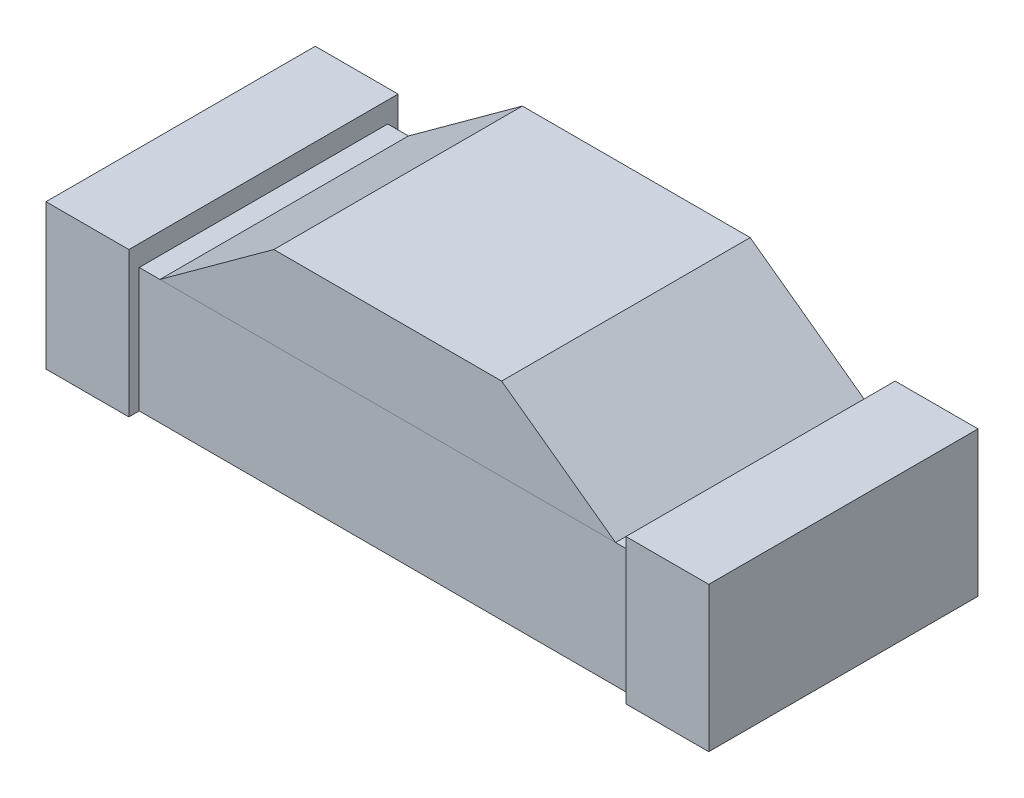
SolidWorks part; units mm, degrees
material "E-Glass Fiber"
ref_plane "Front Plane" through (0, 0, 0) normal (0, 0, 1) x (1, 0, 0)
ref_plane "Top Plane" through (0, 0, 0) normal (0, 1, 0) x (1, 0, 0)
ref_plane "Right Plane" through (0, 0, 0) normal (1, 0, 0) x (0, 0, -1)
sketch "Sketch1" plane through (0, 0, 0) normal (0, 1, 0) x (1, 0, 0)
  line L0 (-55, 0) -> (55, 0) construction
  line L1 (-0.75, 0.3) -> (0.75, 0.3)
  line L2 (-0.75, 0.3) -> (-0.75, 0.125)
  line L3 (-0.75, -0.3) -> (0.75, -0.3)
  line L4 (0.75, 0.3) -> (0.75, 0.125)
  line L5 (0, -55) -> (0, 55) construction
  line L6 (0.75, -0.125) -> (0.75, -0.3)
  line L7 (-0.75, -0.125) -> (-0.75, -0.3)
  arc A0 (-0.75, -0.125) -> (-0.75, 0.125) centre (-0.75, 0) ccw
  arc A1 (0.75, 0.125) -> (0.75, -0.125) centre (0.75, 0) ccw
  dimension "D5" = 0.25
  dimension "D1" = 0.6
  dimension "D2" = 0.3
  dimension "D3" = 1.5
  dimension "D4" = 0.75
extrude "Boss-Extrude1" add sketch "Sketch1" along normal blind 0.3
sketch "Sketch3" plane through (0, 0, 0) normal (0, 0, 1) x (1, 0, 0)
  line L0 (0, 0.8092) -> (0, -0.2421) construction
  line L1 (-0.75, 0.3) -> (0.75, 0.3) construction
  line L2 (0, 0.4) -> (0.2, 0.4)
  line L3 (0, 0.4) -> (0, 0.3)
  line L4 (0, 0.3) -> (0.2, 0.3)
  line L5 (0.2, 0.4) -> (0.2, 0.3)
  dimension "D1" = 0.4
  dimension "D2" = 0.1
revolve "Revolve1" add sketch "Sketch3" angle 360 about L0
sketch "Sketch4" plane through (0, 0, 0) normal (0, 1, 0) x (1, 0, 0)
  line L1 (0, -0.22) -> (0, 0.22) construction
  line L6 (-0.8, 0.325) -> (-0.6, 0.325)
  line L7 (-0.8, 0.325) -> (-0.8, -0.325)
  line L8 (-0.8, -0.325) -> (-0.6, -0.325)
  line L9 (-0.6, 0.325) -> (-0.6, -0.325)
  line L12 (-0.22, 0) -> (0.22, 0) construction
  dimension "D1" = 0.6
  dimension "D2" = 0.2
  dimension "D5" = 0.325
  dimension "D6" = 0.65
extrude "Boss-Extrude4" add sketch "Sketch4" along normal blind 0.35
sketch "Sketch2" plane through (0, 0, 0) normal (0, 0, 1) x (1, 0, 0)
  line L0 (-0.55, 0.3) -> (0.55, 0.3)
  line L1 (-0.6, 0.3) -> (0.75, 0.3) construction
  line L2 (0.55, 0.3) -> (0.275, 0.5)
  line L3 (0.275, 0.5) -> (-0.275, 0.5)
  line L4 (-0.275, 0.5) -> (-0.55, 0.3)
  line L5 (0, -0.22) -> (0, 0.22) construction
  line L6 (0, 0.2805) -> (0, 0.5) construction
  point P10 (0, 0.5)
  dimension "D1" = 0
  dimension "D2" = 0.2
  dimension "D3" = 1.1
  dimension "D4" = 0.55
  dimension "D5" = 0.55
extrude "Boss-Extrude5" add sketch "Sketch2" along normal mid plane 0.6 separate body
mirror "Symétrie1" about plane through (0, 0, 0) normal (1, 0, 0) of "Boss-Extrude4"
